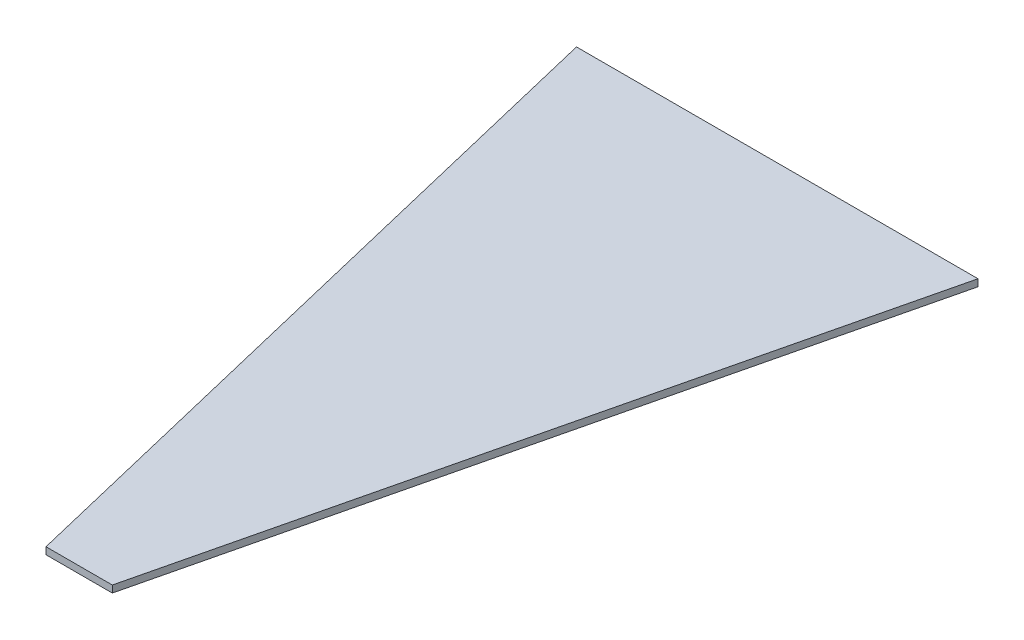
SolidWorks part; units mm, degrees
ref_plane "Front Plane" through (0, 0, 0) normal (0, 0, 1) x (1, 0, 0)
ref_plane "Top Plane" through (0, 0, 0) normal (0, 1, 0) x (1, 0, 0)
ref_plane "Right Plane" through (0, 0, 0) normal (1, 0, 0) x (0, 0, -1)
sketch "Sketch1" plane through (0, 0, 0) normal (0, 1, 0) x (1, 0, 0)
  line L0 (4.75, 0) -> (28.7579, 100)
  line L1 (-55, 0) -> (55, 0) construction
  line L2 (28.7579, 100) -> (-28.7579, 100)
  line L3 (-28.7579, 100) -> (-4.75, 0)
  line L4 (-4.75, 0) -> (4.75, 0)
  line L5 (0, 95.9365) -> (0, -88.5849) construction
  line L6 (0, -55) -> (0, 55) construction
  dimension "D1" = 27
  dimension "D2" = 9.5
  dimension "D3" = 100
extrude "Boss-Extrude1" add sketch "Sketch1" along normal blind 1
